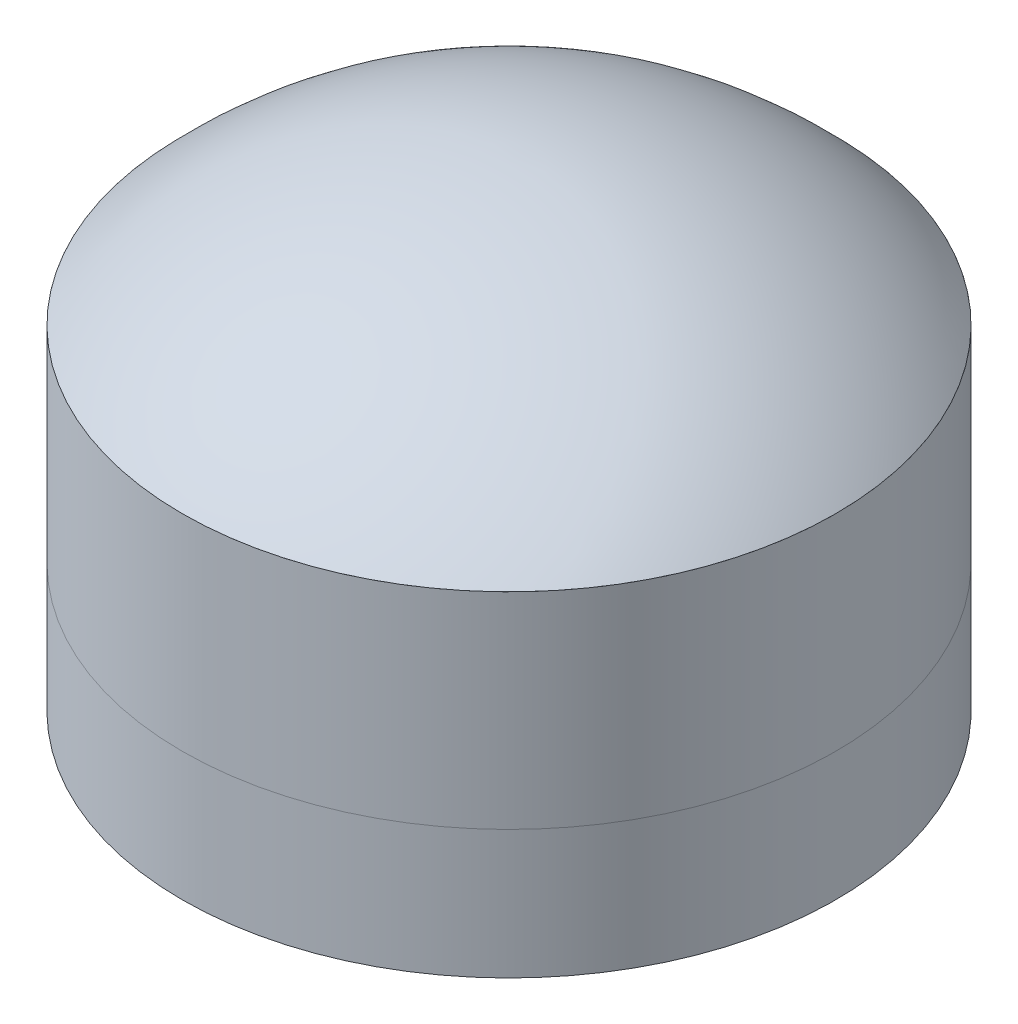
SolidWorks part; units mm, degrees
ref_plane "Front Plane" through (0, 0, 0) normal (0, 0, 1) x (1, 0, 0)
ref_plane "Top Plane" through (0, 0, 0) normal (0, 1, 0) x (1, 0, 0)
ref_plane "Right Plane" through (0, 0, 0) normal (1, 0, 0) x (0, 0, -1)
sketch "Sketch1" plane through (0, 0, 0) normal (0, 1, 0) x (1, 0, 0)
  circle A0 centre (0, 0) radius 6.35
  dimension "D1" = 12.7
extrude "Boss-Extrude1" add sketch "Sketch1" along normal blind 2.5
sketch "Sketch2" plane through (0, 2.5, 0) normal (0, 1, 0) x (1, 0, 0)
  circle A0 centre (0, 0) radius 6.35
  circle A1 centre (0, 0) radius 6.35 construction
extrude "Boss-Extrude2" add sketch "Sketch2" along normal blind 4 separate body
sketch "Sketch3" plane through (0, 0, 0) normal (0, 0, 1) x (1, 0, 0)
  line L0 (6.35, 6.5) -> (-6.35, 6.5) construction
  line L1 (6.35, 6.5) -> (0, 6.5)
  line L2 (0, 6.5) -> (0, 9.2363)
  arc A0 (6.35, 6.5) -> (0, 9.2363) centre (0, 0.5) ccw
  point P0 (0, 6.5)
  dimension "D1" = 6
  dimension "D2" = 6.35
ref_axis "Axis1" through (0, 8.4215, 0) along (0, -1, 0)
revolve "Revolve1" add sketch "Sketch3" angle 360 about axis through (0, 8.4215, 0) along (0, -1, 0)
